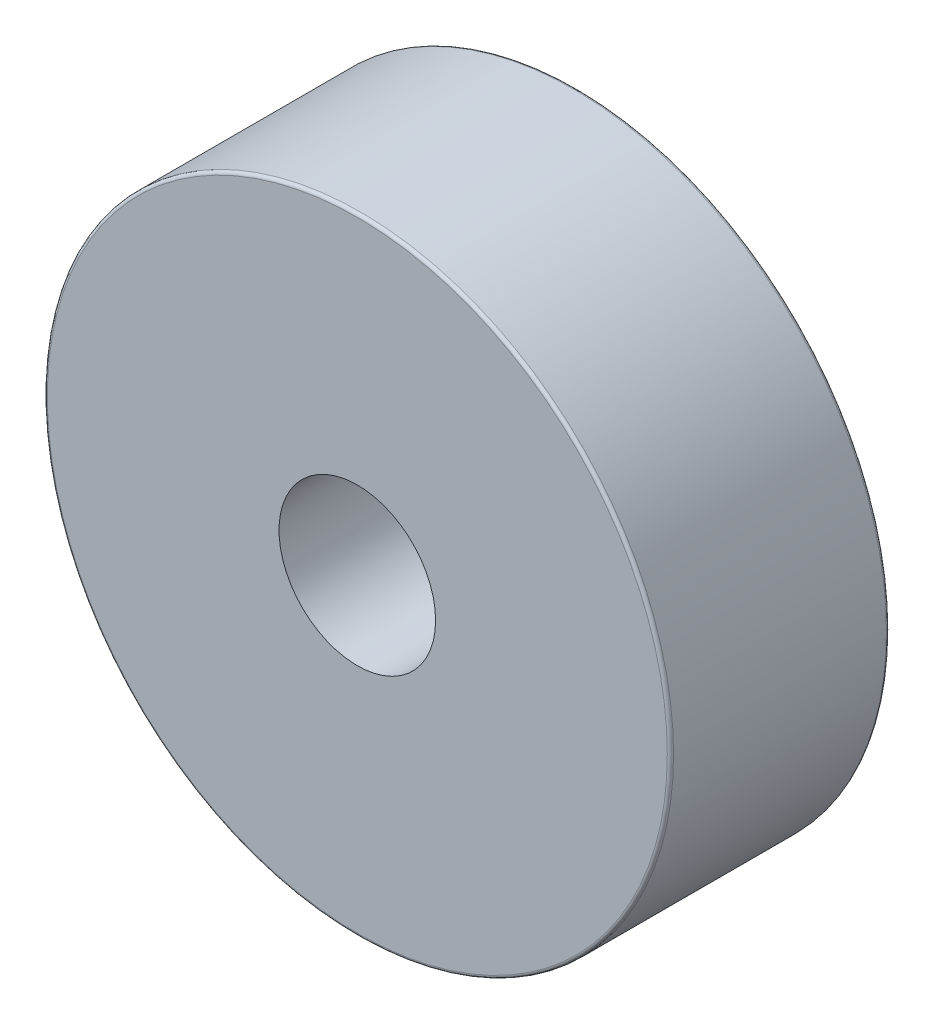
SolidWorks part; units mm, degrees
material "尼龙 101"
ref_plane "前视基准面" through (0, 0, 0) normal (0, 0, 1) x (1, 0, 0)
ref_plane "上视基准面" through (0, 0, 0) normal (0, 1, 0) x (1, 0, 0)
ref_plane "右视基准面" through (0, 0, 0) normal (1, 0, 0) x (0, 0, -1)
sketch "草图1" plane through (0, 0, 0) normal (0, 0, 1) x (1, 0, 0)
  circle A0 centre (0, 0) radius 10
  circle A1 centre (0, 0) radius 2.5
  dimension "D1" = 5
  dimension "D2" = 20
extrude "凸台-拉伸1" add sketch "草图1" along normal blind 7
fillet "圆角1" radius 0.1 2 edges at (10, 0, 7) (10, 0, 0)
